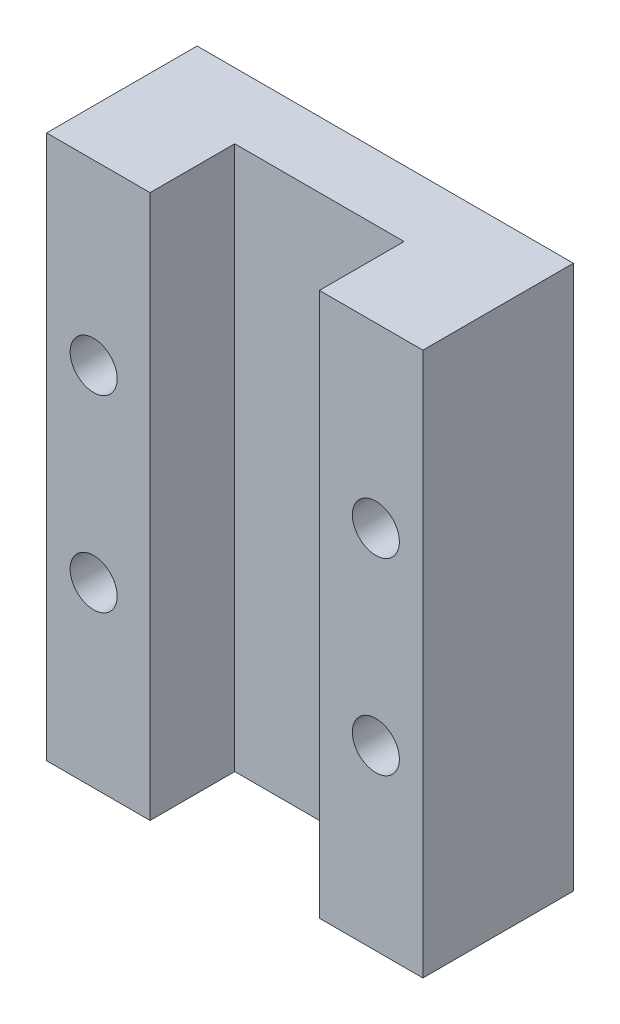
SolidWorks part; units mm, degrees
ref_plane "前视基准面" through (0, 0, 0) normal (0, 0, 1) x (1, 0, 0)
ref_plane "上视基准面" through (0, 0, 0) normal (0, 1, 0) x (1, 0, 0)
ref_plane "右视基准面" through (0, 0, 0) normal (1, 0, 0) x (0, 0, -1)
sketch "草图1" plane through (0, 0, 0) normal (0, 0, 1) x (1, 0, 0)
  line L1 (0, 0) -> (20, 0)
  line L2 (0, 0) -> (0, 28.9)
  line L3 (0, 28.9) -> (20, 28.9)
  line L4 (20, 0) -> (20, 28.9)
  dimension "D1" = 20
  dimension "D2" = 28.9
extrude "凸台-拉伸1" add sketch "草图1" along normal blind 8
sketch "草图2" plane through (0, 28.9, 0) normal (0, 1, 0) x (1, 0, 0)
  line L0 (10, -8) -> (10, 12.1383) construction
  line L1 (20, -8) -> (0, -8) construction
  line L2 (20, 0) -> (0, 0) construction
  line L3 (5.5, -8) -> (14.5, -8)
  line L4 (5.5, -8) -> (5.5, -3.5)
  line L5 (5.5, -3.5) -> (14.5, -3.5)
  line L6 (14.5, -8) -> (14.5, -3.5)
  dimension "D1" = 3.5
  dimension "D2" = 9
extrude "切除-拉伸1" cut sketch "草图2" against normal through all
hole_wizard "M3 螺纹孔1" positions "草图3" profile "草图5" tap size "M3" standard "ISO"
sketch "草图3" plane through (0, 0, 0) normal (0, 0, -1) x (-1, 0, 0)
  line L0 (-10, 0) -> (-10, 28.9) construction
  line L1 (0, 0) -> (-20, 0) construction
  line L2 (-20, 28.9) -> (0, 28.9) construction
  line L3 (-10, 28.9) -> (-10, 14.45) construction
  line L4 (-10, 14.45) -> (-23.8351, 14.45) construction
  point P0 (-2.5, 9.45)
  point P2 (-17.5, 9.45)
  point P4 (-2.5, 19.45)
  point P6 (-17.5, 19.45)
  dimension "D1" = 15
  dimension "D2" = 10
sketch "草图5" plane through (2.5, 9.45, 0) normal (1, 0, 0) x (0, 1, 0)
  line L0 (0, 0) -> (0, 10.8511)
  line L1 (0, 10.8511) -> (1.25, 10.1)
  line L2 (1.25, 10.1) -> (1.25, 0)
  line L5 (1.25, 0) -> (0, 0)
  line L10 (0, 10.8511) -> (-1.25, 10.1) construction
  line L11 (0, -6.35) -> (0, 107.95) construction
  dimension "螺纹孔钻头直径" = 2.5
  dimension "螺纹孔钻头深度" = 10.1
  dimension "导头角度" = 118
cosmetic thread "孔螺蚊线1" parameters "D1"=6, "D2"=3
cosmetic thread "孔螺蚊线2" parameters "D1"=6, "D2"=3
cosmetic thread "孔螺蚊线3" parameters "D1"=6, "D2"=3
cosmetic thread "孔螺蚊线4" parameters "D1"=6, "D2"=3
